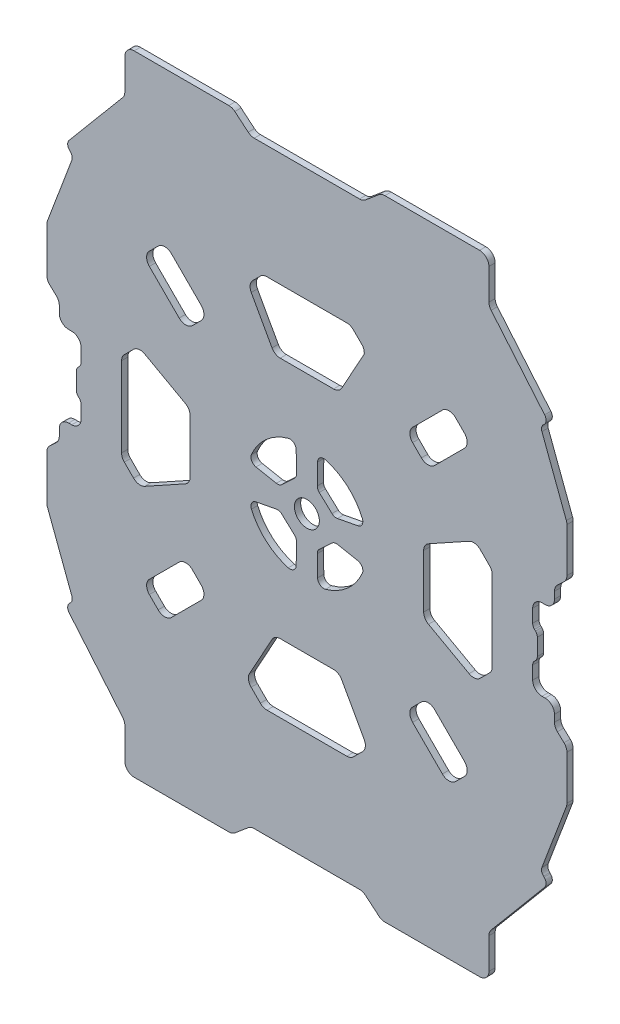
SolidWorks part; units mm, degrees
ref_plane "Piano frontale" through (0, 0, 0) normal (0, 0, 1) x (1, 0, 0)
ref_plane "Piano superiore" through (0, 0, 0) normal (0, 1, 0) x (1, 0, 0)
ref_plane "Piano destro" through (0, 0, 0) normal (1, 0, 0) x (0, 0, -1)
sketch "Schizzo1" plane through (0, 0, 0) normal (0, 0, 1) x (1, 0, 0)
  line L1 (-101.8101, -19.1121) -> (-101.8101, -13.7689)
  line L2 (-101.2243, -12.3547) -> (-100.8959, -12.0263)
  line L3 (-100.3101, -10.6121) -> (-100.3101, -6.4405)
  line L4 (-103.3101, -3.4405) -> (-104.3101, -3.4405)
  line L5 (-107.3101, -0.4405) -> (-107.3101, 1.7657)
  line L6 (-108.2511, 3.9475) -> (-110.3692, 5.9463)
  line L7 (-111.3101, 8.1282) -> (-111.3101, 22.2883)
  line L8 (-111.1177, 23.3454) -> (-103.2791, 44.1649)
  line L9 (-103.7782, 46.3242) -> (-103.9835, 46.518)
  line L10 (-104.1429, 49.2581) -> (-86.9708, 69.723)
  line L11 (-86.2689, 71.6514) -> (-86.2689, 81.5595)
  line L12 (-83.2689, 84.5595) -> (-52.8608, 84.5595)
  line L13 (-50.9324, 83.8576) -> (-46.6466, 80.2614)
  line L14 (-44.7182, 79.5595) -> (-10.902, 79.5595)
  line L16 (-87.3101, -29.2596) -> (-87.3101, -3.6215)
  line L17 (-86.4314, -1.5001) -> (-83.4693, 1.462)
  line L18 (-79.8952, 1.9655) -> (-66.8574, -5.2505)
  line L19 (-65.3101, -7.8753) -> (-65.3101, -25.0057)
  line L21 (-78.3926, 31.3073) -> (-75.5579, 34.142)
  line L22 (-71.3153, 34.142) -> (-61.7481, 24.5748)
  line L23 (-61.7481, 20.3322) -> (-64.5828, 17.4975)
  line L24 (-68.8254, 17.4975) -> (-78.3926, 27.0646)
  line L25 (-44.1535, -11.5906) -> (-37.6069, -12.8452)
  line L26 (-35.8643, -12.3416) -> (-31.7768, -8.5186)
  line L27 (-31.1432, -7.0279) -> (-31.2436, -0.3343)
  line L30 (-36.3754, 22.5595) -> (-19.2449, 22.5595)
  line L31 (-45.6817, 36.179) -> (-39.0002, 24.1068)
  line L32 (-42.7505, 42.1808) -> (-45.1783, 39.7531)
  line L33 (-14.9911, 43.0595) -> (-40.6292, 43.0595)
  line L36 (-12.8698, 42.1808) -> (-9.9076, 39.2186)
  line L37 (-9.4041, 37.1446) -> (-16.6201, 24.1068)
  line L38 (-24.477, -7.0279) -> (-24.3767, -0.3343)
  line L39 (-19.756, -12.3416) -> (-23.8434, -8.5186)
  line L40 (-11.4668, -11.5906) -> (-18.0134, -12.8452)
  line L41 (13.2052, 17.4975) -> (22.7723, 27.0646)
  line L42 (6.1279, 20.3322) -> (8.9626, 17.4975)
  line L43 (15.695, 34.142) -> (6.1279, 24.5748)
  line L44 (22.7723, 31.3073) -> (19.9377, 34.142)
  line L46 (9.6899, -7.8753) -> (9.6899, -25.0057)
  line L47 (24.275, 1.9655) -> (11.2371, -5.2505)
  line L48 (30.8112, -1.5001) -> (27.849, 1.462)
  line L49 (31.6899, -29.2596) -> (31.6899, -3.6215)
  line L50 (-4.6878, 83.8576) -> (-8.9737, 80.2614)
  line L51 (27.6486, 84.5595) -> (-2.7594, 84.5595)
  line L52 (30.6486, 71.6514) -> (30.6486, 81.5595)
  line L53 (48.5226, 49.2581) -> (31.3505, 69.723)
  line L54 (48.1579, 46.3242) -> (48.3632, 46.518)
  line L55 (55.4975, 23.3454) -> (47.6589, 44.1649)
  line L56 (55.6899, 8.1282) -> (55.6899, 22.2883)
  line L57 (52.6308, 3.9475) -> (54.7489, 5.9463)
  line L58 (51.6899, -0.4405) -> (51.6899, 1.7657)
  line L59 (47.6899, -3.4405) -> (48.6899, -3.4405)
  line L60 (44.6899, -10.6121) -> (44.6899, -6.4405)
  line L61 (45.6041, -12.3547) -> (45.2757, -12.0263)
  line L62 (46.1899, -19.1121) -> (46.1899, -13.7689)
  line L65 (45.6041, -20.5263) -> (45.2757, -20.8547)
  line L66 (44.6899, -22.2689) -> (44.6899, -26.4405)
  line L67 (47.6899, -29.4405) -> (48.6899, -29.4405)
  line L68 (51.6899, -32.4405) -> (51.6899, -34.6467)
  line L69 (52.6308, -36.8285) -> (54.7489, -38.8273)
  line L70 (55.6899, -41.0092) -> (55.6899, -55.1693)
  line L71 (55.4975, -56.2264) -> (47.6589, -77.046)
  line L72 (48.1579, -79.2052) -> (48.3632, -79.399)
  line L73 (48.5226, -82.1391) -> (31.3505, -102.6041)
  line L74 (30.6486, -104.5324) -> (30.6486, -114.4405)
  line L75 (27.6486, -117.4405) -> (-2.7594, -117.4405)
  line L76 (-4.6878, -116.7386) -> (-8.9737, -113.1424)
  line L77 (30.8112, -31.3809) -> (27.849, -34.3431)
  line L78 (24.275, -34.8465) -> (11.2371, -27.6305)
  line L79 (22.7723, -64.1883) -> (19.9377, -67.023)
  line L80 (15.695, -67.023) -> (6.1279, -57.4558)
  line L81 (6.1279, -53.2132) -> (8.9626, -50.3785)
  line L82 (13.2052, -50.3785) -> (22.7723, -59.9457)
  line L83 (-11.4668, -21.2904) -> (-18.0134, -20.0358)
  line L84 (-19.756, -20.5394) -> (-23.8434, -24.3624)
  line L85 (-24.477, -25.8531) -> (-24.3767, -32.5468)
  line L86 (-9.4041, -70.0256) -> (-16.6201, -56.9878)
  line L87 (-12.8698, -76.5618) -> (-9.9076, -73.5997)
  line L89 (-14.9911, -77.4405) -> (-40.6292, -77.4405)
  line L90 (-42.7505, -76.5618) -> (-45.7127, -73.5997)
  line L91 (-46.2161, -70.0256) -> (-39.0002, -56.9878)
  line L92 (-36.3754, -55.4405) -> (-19.2449, -55.4405)
  line L93 (-31.1432, -25.8531) -> (-31.2436, -32.5468)
  line L94 (-35.8643, -20.5394) -> (-31.7768, -24.3624)
  line L95 (-44.1535, -21.2904) -> (-37.6069, -20.0358)
  line L96 (-68.8254, -50.3785) -> (-78.3926, -59.9457)
  line L97 (-61.7481, -53.2132) -> (-64.5828, -50.3785)
  line L98 (-71.3153, -67.023) -> (-61.7481, -57.4558)
  line L99 (-78.3926, -64.1883) -> (-75.5579, -67.023)
  line L100 (-79.8952, -34.8465) -> (-66.8574, -27.6305)
  line L101 (-86.4314, -31.3809) -> (-83.4693, -34.3431)
  line L102 (-44.7182, -112.4405) -> (-10.902, -112.4405)
  line L103 (-50.9324, -116.7386) -> (-46.6466, -113.1424)
  line L104 (-83.2689, -117.4405) -> (-52.8608, -117.4405)
  line L105 (-86.2689, -104.5324) -> (-86.2689, -114.4405)
  line L106 (-104.1429, -82.1391) -> (-86.9708, -102.6041)
  line L107 (-103.7782, -79.2052) -> (-103.9835, -79.399)
  line L108 (-111.1177, -56.2264) -> (-103.2791, -77.046)
  line L109 (-111.3101, -41.0092) -> (-111.3101, -55.1693)
  line L110 (-108.2511, -36.8285) -> (-110.3692, -38.8273)
  line L111 (-107.3101, -32.4405) -> (-107.3101, -34.6467)
  line L112 (-103.3101, -29.4405) -> (-104.3101, -29.4405)
  line L113 (-100.3101, -22.2689) -> (-100.3101, -26.4405)
  line L114 (-101.2243, -20.5263) -> (-100.8959, -20.8547)
  arc A0 (-45.6154, -8.8386) -> (-33.7894, 1.5598) centre (-28.7923, -16.0474) cw
  arc A1 (-42.7505, 42.1808) -> (-40.6292, 43.0595) centre (-40.6292, 40.0595) cw
  arc A2 (-45.6817, 36.179) -> (-45.1783, 39.7531) centre (-43.0569, 37.6317) cw
  arc A3 (-36.3754, 22.5595) -> (-39.0002, 24.1068) centre (-36.3754, 25.5595) cw
  arc A4 (-66.8574, -5.2505) -> (-65.3101, -7.8753) centre (-68.3101, -7.8753) cw
  arc A5 (-83.4693, 1.462) -> (-79.8952, 1.9655) centre (-81.348, -0.6593) cw
  arc A6 (-87.3101, -3.6215) -> (-86.4314, -1.5001) centre (-84.3101, -3.6215) cw
  arc A7 (-64.5828, 17.4975) -> (-68.8254, 17.4975) centre (-66.7041, 19.6188) cw
  arc A8 (-61.7481, 24.5748) -> (-61.7481, 20.3322) centre (-63.8694, 22.4535) cw
  arc A9 (-75.5579, 34.142) -> (-71.3153, 34.142) centre (-73.4366, 32.0206) cw
  arc A10 (-78.3926, 31.3073) -> (-78.3926, 27.0646) centre (-76.2713, 29.186) ccw
  arc A11 (-46.6466, 80.2614) -> (-44.7182, 79.5595) centre (-44.7182, 82.5595) ccw
  arc A12 (-52.8608, 84.5595) -> (-50.9324, 83.8576) centre (-52.8608, 81.5595) cw
  arc A13 (-86.2689, 81.5595) -> (-83.2689, 84.5595) centre (-83.2689, 81.5595) cw
  arc A14 (-86.9708, 69.723) -> (-86.2689, 71.6514) centre (-89.2689, 71.6514) ccw
  arc A15 (-111.3101, 22.2883) -> (-111.1177, 23.3454) centre (-108.3101, 22.2883) cw
  arc A16 (-110.3692, 5.9463) -> (-111.3101, 8.1282) centre (-108.3101, 8.1282) cw
  arc A17 (-107.3101, 1.7657) -> (-108.2511, 3.9475) centre (-110.3101, 1.7657) ccw
  arc A18 (-104.3101, -3.4405) -> (-107.3101, -0.4405) centre (-104.3101, -0.4405) cw
  arc A19 (-100.3101, -6.4405) -> (-103.3101, -3.4405) centre (-103.3101, -6.4405) ccw
  arc A20 (-37.6069, -12.8452) -> (-35.8643, -12.3416) centre (-37.2304, -10.8809) ccw
  arc A21 (-31.7768, -8.5186) -> (-31.1432, -7.0279) centre (-33.143, -7.0579) ccw
  arc A22 (-31.2436, -0.3343) -> (-33.7894, 1.5598) centre (-33.2434, -0.3643) ccw
  arc A23 (-44.1535, -11.5906) -> (-45.6154, -8.8386) centre (-43.7771, -9.6264) cw
  arc A24 (-101.8101, -13.7689) -> (-101.2243, -12.3547) centre (-99.8101, -13.7689) cw
  arc A25 (-100.8959, -12.0263) -> (-100.3101, -10.6121) centre (-102.3101, -10.6121) ccw
  arc A26 (-103.9835, 46.518) -> (-104.1429, 49.2581) centre (-102.6108, 47.9725) cw
  arc A27 (-103.2791, 44.1649) -> (-103.7782, 46.3242) centre (-105.1509, 44.8696) ccw
  arc A28 (47.6589, 44.1649) -> (48.1579, 46.3242) centre (49.5306, 44.8696) cw
  arc A29 (48.3632, 46.518) -> (48.5226, 49.2581) centre (46.9906, 47.9725) ccw
  arc A30 (45.2757, -12.0263) -> (44.6899, -10.6121) centre (46.6899, -10.6121) cw
  arc A31 (46.1899, -13.7689) -> (45.6041, -12.3547) centre (44.1899, -13.7689) ccw
  arc A32 (-11.4668, -11.5906) -> (-10.0049, -8.8386) centre (-11.8432, -9.6264) ccw
  arc A33 (-24.3767, -0.3343) -> (-21.8308, 1.5598) centre (-22.3769, -0.3643) cw
  arc A34 (-23.8434, -8.5186) -> (-24.477, -7.0279) centre (-22.4773, -7.0579) cw
  arc A35 (-18.0134, -12.8452) -> (-19.756, -12.3416) centre (-18.3898, -10.8809) cw
  arc A36 (44.6899, -6.4405) -> (47.6899, -3.4405) centre (47.6899, -6.4405) cw
  arc A37 (48.6899, -3.4405) -> (51.6899, -0.4405) centre (48.6899, -0.4405) ccw
  arc A38 (51.6899, 1.7657) -> (52.6308, 3.9475) centre (54.6899, 1.7657) cw
  arc A39 (54.7489, 5.9463) -> (55.6899, 8.1282) centre (52.6899, 8.1282) ccw
  arc A40 (55.6899, 22.2883) -> (55.4975, 23.3454) centre (52.6899, 22.2883) ccw
  arc A41 (31.3505, 69.723) -> (30.6486, 71.6514) centre (33.6486, 71.6514) cw
  arc A42 (30.6486, 81.5595) -> (27.6486, 84.5595) centre (27.6486, 81.5595) ccw
  arc A43 (-2.7594, 84.5595) -> (-4.6878, 83.8576) centre (-2.7594, 81.5595) ccw
  arc A44 (-8.9737, 80.2614) -> (-10.902, 79.5595) centre (-10.902, 82.5595) cw
  arc A45 (22.7723, 31.3073) -> (22.7723, 27.0646) centre (20.651, 29.186) cw
  arc A46 (19.9377, 34.142) -> (15.695, 34.142) centre (17.8163, 32.0206) ccw
  arc A47 (6.1279, 24.5748) -> (6.1279, 20.3322) centre (8.2492, 22.4535) ccw
  arc A48 (8.9626, 17.4975) -> (13.2052, 17.4975) centre (11.0839, 19.6188) ccw
  arc A49 (31.6899, -3.6215) -> (30.8112, -1.5001) centre (28.6899, -3.6215) ccw
  arc A50 (27.849, 1.462) -> (24.275, 1.9655) centre (25.7277, -0.6593) ccw
  arc A51 (11.2371, -5.2505) -> (9.6899, -7.8753) centre (12.6899, -7.8753) ccw
  arc A52 (-19.2449, 22.5595) -> (-16.6201, 24.1068) centre (-19.2449, 25.5595) ccw
  arc A53 (-9.4041, 37.1446) -> (-9.9076, 39.2186) centre (-12.3805, 37.5202) ccw
  arc A54 (-12.8698, 42.1808) -> (-14.9911, 43.0595) centre (-14.9911, 40.0595) ccw
  arc A55 (-10.0049, -8.8386) -> (-21.8308, 1.5598) centre (-26.828, -16.0474) ccw
  arc A56 (-10.0049, -24.0424) -> (-21.8308, -34.4408) centre (-26.828, -16.8336) cw
  arc A57 (-12.8698, -76.5618) -> (-14.9911, -77.4405) centre (-14.9911, -74.4405) cw
  arc A58 (-9.4041, -70.0256) -> (-9.9076, -73.5997) centre (-12.0289, -71.4783) cw
  arc A59 (-19.2449, -55.4405) -> (-16.6201, -56.9878) centre (-19.2449, -58.4405) cw
  arc A60 (11.2371, -27.6305) -> (9.6899, -25.0057) centre (12.6899, -25.0057) cw
  arc A61 (27.849, -34.3431) -> (24.275, -34.8465) centre (25.7277, -32.2217) cw
  arc A62 (31.6899, -29.2596) -> (30.8112, -31.3809) centre (28.6899, -29.2596) cw
  arc A63 (8.9626, -50.3785) -> (13.2052, -50.3785) centre (11.0839, -52.4998) cw
  arc A64 (6.1279, -57.4558) -> (6.1279, -53.2132) centre (8.2492, -55.3345) cw
  arc A65 (19.9377, -67.023) -> (15.695, -67.023) centre (17.8163, -64.9017) cw
  arc A66 (22.7723, -64.1883) -> (22.7723, -59.9457) centre (20.651, -62.067) ccw
  arc A67 (-8.9737, -113.1424) -> (-10.902, -112.4405) centre (-10.902, -115.4405) ccw
  arc A68 (-2.7594, -117.4405) -> (-4.6878, -116.7386) centre (-2.7594, -114.4405) cw
  arc A69 (30.6486, -114.4405) -> (27.6486, -117.4405) centre (27.6486, -114.4405) cw
  arc A70 (31.3505, -102.6041) -> (30.6486, -104.5324) centre (33.6486, -104.5324) ccw
  arc A71 (55.6899, -55.1693) -> (55.4975, -56.2264) centre (52.6899, -55.1693) cw
  arc A72 (54.7489, -38.8273) -> (55.6899, -41.0092) centre (52.6899, -41.0092) cw
  arc A73 (51.6899, -34.6467) -> (52.6308, -36.8285) centre (54.6899, -34.6467) ccw
  arc A74 (48.6899, -29.4405) -> (51.6899, -32.4405) centre (48.6899, -32.4405) cw
  arc A75 (44.6899, -26.4405) -> (47.6899, -29.4405) centre (47.6899, -26.4405) ccw
  arc A76 (-18.0134, -20.0358) -> (-19.756, -20.5394) centre (-18.3898, -22.0001) ccw
  arc A77 (-23.8434, -24.3624) -> (-24.477, -25.8531) centre (-22.4773, -25.8231) ccw
  arc A78 (-24.3767, -32.5468) -> (-21.8308, -34.4408) centre (-22.3769, -32.5168) ccw
  arc A79 (-11.4668, -21.2904) -> (-10.0049, -24.0424) centre (-11.8432, -23.2546) cw
  arc A80 (46.1899, -19.1121) -> (45.6041, -20.5263) centre (44.1899, -19.1121) cw
  arc A81 (45.2757, -20.8547) -> (44.6899, -22.2689) centre (46.6899, -22.2689) ccw
  arc A82 (48.3632, -79.399) -> (48.5226, -82.1391) centre (46.9906, -80.8535) cw
  arc A83 (47.6589, -77.046) -> (48.1579, -79.2052) centre (49.5306, -77.7507) ccw
  arc A84 (-103.2791, -77.046) -> (-103.7782, -79.2052) centre (-105.1509, -77.7507) cw
  arc A85 (-103.9835, -79.399) -> (-104.1429, -82.1391) centre (-102.6108, -80.8535) ccw
  arc A86 (-100.8959, -20.8547) -> (-100.3101, -22.2689) centre (-102.3101, -22.2689) cw
  arc A87 (-101.8101, -19.1121) -> (-101.2243, -20.5263) centre (-99.8101, -19.1121) ccw
  arc A88 (-44.1535, -21.2904) -> (-45.6154, -24.0424) centre (-43.7771, -23.2546) ccw
  arc A89 (-31.2436, -32.5468) -> (-33.7894, -34.4408) centre (-33.2434, -32.5168) cw
  arc A90 (-31.7768, -24.3624) -> (-31.1432, -25.8531) centre (-33.143, -25.8231) cw
  arc A91 (-37.6069, -20.0358) -> (-35.8643, -20.5394) centre (-37.2304, -22.0001) cw
  arc A92 (-100.3101, -26.4405) -> (-103.3101, -29.4405) centre (-103.3101, -26.4405) cw
  arc A93 (-104.3101, -29.4405) -> (-107.3101, -32.4405) centre (-104.3101, -32.4405) ccw
  arc A94 (-107.3101, -34.6467) -> (-108.2511, -36.8285) centre (-110.3101, -34.6467) cw
  arc A95 (-110.3692, -38.8273) -> (-111.3101, -41.0092) centre (-108.3101, -41.0092) ccw
  arc A96 (-111.3101, -55.1693) -> (-111.1177, -56.2264) centre (-108.3101, -55.1693) ccw
  arc A97 (-86.9708, -102.6041) -> (-86.2689, -104.5324) centre (-89.2689, -104.5324) cw
  arc A98 (-86.2689, -114.4405) -> (-83.2689, -117.4405) centre (-83.2689, -114.4405) ccw
  arc A99 (-52.8608, -117.4405) -> (-50.9324, -116.7386) centre (-52.8608, -114.4405) ccw
  arc A100 (-46.6466, -113.1424) -> (-44.7182, -112.4405) centre (-44.7182, -115.4405) cw
  arc A101 (-78.3926, -64.1883) -> (-78.3926, -59.9457) centre (-76.2713, -62.067) cw
  arc A102 (-75.5579, -67.023) -> (-71.3153, -67.023) centre (-73.4366, -64.9017) ccw
  arc A103 (-61.7481, -57.4558) -> (-61.7481, -53.2132) centre (-63.8694, -55.3345) ccw
  arc A104 (-64.5828, -50.3785) -> (-68.8254, -50.3785) centre (-66.7041, -52.4998) ccw
  arc A105 (-87.3101, -29.2596) -> (-86.4314, -31.3809) centre (-84.3101, -29.2596) ccw
  arc A106 (-83.4693, -34.3431) -> (-79.8952, -34.8465) centre (-81.348, -32.2217) ccw
  arc A107 (-66.8574, -27.6305) -> (-65.3101, -25.0057) centre (-68.3101, -25.0057) ccw
  arc A108 (-36.3754, -55.4405) -> (-39.0002, -56.9878) centre (-36.3754, -58.4405) ccw
  arc A109 (-46.2161, -70.0256) -> (-45.7127, -73.5997) centre (-43.5913, -71.4783) ccw
  arc A110 (-42.7505, -76.5618) -> (-40.6292, -77.4405) centre (-40.6292, -74.4405) ccw
  arc A111 (-45.6154, -24.0424) -> (-33.7894, -34.4408) centre (-28.7923, -16.8336) ccw
  circle A112 centre (-27.8101, -16.4405) radius 4
  point P1 (-27.8101, 22.5595)
  point P14 (-27.8101, -55.4405)
  point P27 (-63.1655, 18.9148)
  point P30 (-33.8205, -10.4301)
  point P40 (-41.8718, 43.0595)
  point P43 (-46.7757, 38.1556)
  point P46 (-38.1438, 22.5595)
  point P49 (-65.3101, -6.1068)
  point P52 (-81.8718, 3.0595)
  point P55 (-87.3101, -2.3788)
  point P66 (-45.8101, 79.5595)
  point P69 (-51.7689, 84.5595)
  point P72 (-86.2689, 84.5595)
  point P75 (-86.2689, 70.5595)
  point P78 (-111.3101, 22.8343)
  point P81 (-111.3101, 6.8343)
  point P84 (-107.3101, 3.0595)
  point P87 (-107.3101, -3.4405)
  point P90 (-100.3101, -3.4405)
  point P93 (-36.6074, -13.0367)
  point P96 (-31.1299, -7.9136)
  point P99 (-31.2799, 2.0853)
  point P102 (-46.4287, -11.1546)
  point P105 (-101.8101, -12.9405)
  point P108 (-100.3101, -11.4405)
  point P111 (-105.3556, 47.8128)
  point P114 (-102.8101, 45.4106)
  point P201 (47.1899, 45.4106)
  point P202 (49.7354, 47.8128)
  point P203 (44.6899, -11.4405)
  point P204 (46.1899, -12.9405)
  point P205 (-9.1915, -11.1546)
  point P206 (-24.3404, 2.0853)
  point P207 (-24.4903, -7.9136)
  point P208 (-19.0128, -13.0367)
  point P209 (44.6899, -3.4405)
  point P210 (51.6899, -3.4405)
  point P211 (51.6899, 3.0595)
  point P212 (55.6899, 6.8343)
  point P213 (55.6899, 22.8343)
  point P214 (30.6486, 70.5595)
  point P215 (30.6486, 84.5595)
  point P216 (-3.8514, 84.5595)
  point P217 (-9.8101, 79.5595)
  point P218 (31.6899, -2.3788)
  point P219 (26.2516, 3.0595)
  point P220 (9.6899, -6.1068)
  point P221 (-17.4765, 21.0595)
  point P222 (-8.3101, 37.6212)
  point P223 (-13.7484, 43.0595)
  point P224 (-21.7997, -10.4301)
  point P225 (7.5452, 18.9148)
  point P226 (7.5452, -51.7958)
  point P227 (-21.7997, -22.4509)
  point P228 (-13.7484, -75.9405)
  point P229 (-8.3101, -70.5022)
  point P230 (-17.4765, -53.9405)
  point P231 (9.6899, -26.7742)
  point P232 (26.2516, -35.9405)
  point P233 (31.6899, -30.5022)
  point P234 (-9.8101, -112.4405)
  point P235 (-3.8514, -117.4405)
  point P236 (30.6486, -117.4405)
  point P237 (30.6486, -103.4405)
  point P238 (55.6899, -55.7154)
  point P239 (55.6899, -39.7154)
  point P240 (51.6899, -35.9405)
  point P241 (51.6899, -29.4405)
  point P242 (44.6899, -29.4405)
  point P243 (-19.0128, -19.8443)
  point P244 (-24.4903, -24.9675)
  point P245 (-24.3404, -34.9663)
  point P246 (-9.1915, -21.7264)
  point P247 (46.1899, -19.9405)
  point P248 (44.6899, -21.4405)
  point P249 (49.7354, -80.6939)
  point P250 (47.1899, -78.2917)
  point P251 (-102.8101, -78.2917)
  point P252 (-105.3556, -80.6939)
  point P253 (-100.3101, -21.4405)
  point P254 (-101.8101, -19.9405)
  point P255 (-46.4287, -21.7264)
  point P256 (-31.2799, -34.9663)
  point P257 (-31.1299, -24.9675)
  point P258 (-36.6074, -19.8443)
  point P259 (-100.3101, -29.4405)
  point P260 (-107.3101, -29.4405)
  point P261 (-107.3101, -35.9405)
  point P262 (-111.3101, -39.7154)
  point P263 (-111.3101, -55.7154)
  point P264 (-86.2689, -103.4405)
  point P265 (-86.2689, -117.4405)
  point P266 (-51.7689, -117.4405)
  point P267 (-45.8101, -112.4405)
  point P268 (-87.3101, -30.5022)
  point P269 (-81.8718, -35.9405)
  point P270 (-65.3101, -26.7742)
  point P271 (-38.1438, -53.9405)
  point P272 (-47.3101, -70.5022)
  point P273 (-41.8718, -75.9405)
  point P274 (-33.8205, -22.4509)
  point P275 (-63.1655, -51.7958)
  dimension "D25" = 3
  dimension "D26" = 2
  dimension "D10" = 8
  dimension "D2" = 1.5
  dimension "D3" = 8
  dimension "D4" = 7
  dimension "D5" = 6.5
  dimension "D6" = 4
  dimension "D7" = 16
  dimension "D8" = 8.5
  dimension "D9" = 3.5
  dimension "D11" = 14
  dimension "D12" = 34.5
  dimension "D13" = 5
  dimension "D14" = 39
  dimension "D15" = 39
  dimension "D20" = 10
  dimension "D21" = 10
  dimension "D22" = 7.5
  dimension "D23" = 8.5
  dimension "D24" = 50
extrude "Estrusione-Estrusione1" add sketch "Schizzo1" along normal blind 2
